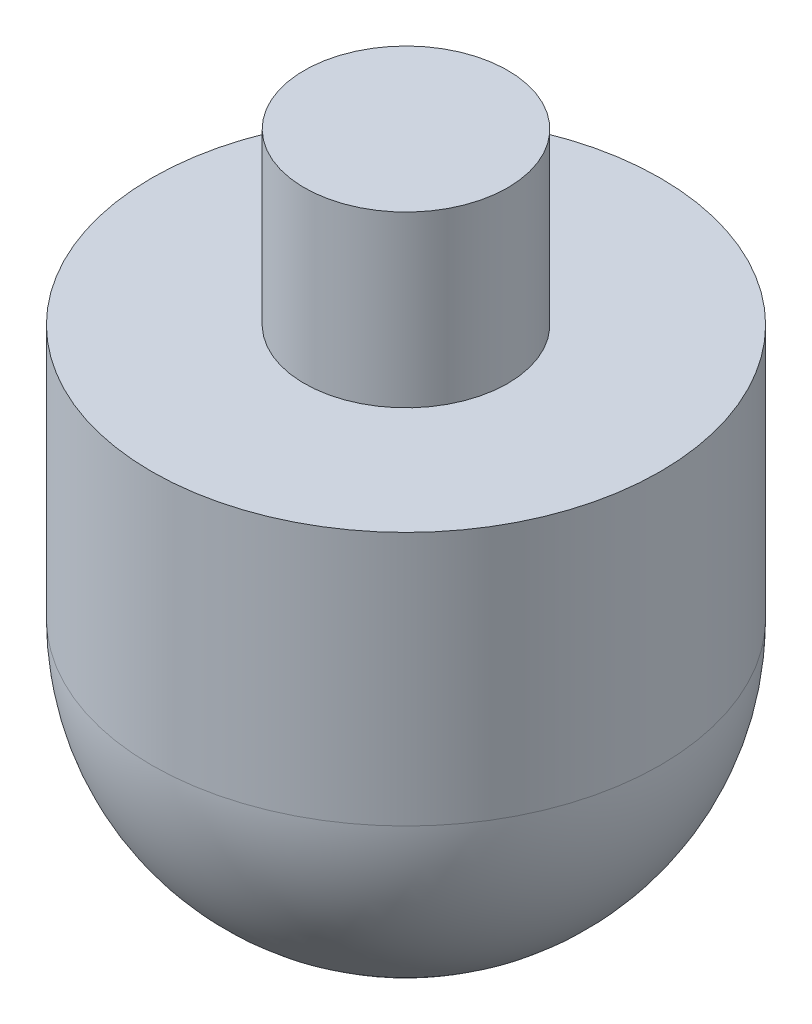
SolidWorks part; units mm, degrees
ref_plane "Front Plane" through (0, 0, 0) normal (0, 0, 1) x (1, 0, 0)
ref_plane "Top Plane" through (0, 0, 0) normal (0, 1, 0) x (1, 0, 0)
ref_plane "Right Plane" through (0, 0, 0) normal (1, 0, 0) x (0, 0, -1)
sketch "Sketch1" plane through (0, 0, 0) normal (0, 0, 1) x (1, 0, 0)
  line L0 (0, 25) -> (0, 41.3952) construction
  line L1 (0, 25) -> (0, -15)
  line L2 (15, 0) -> (15, 15)
  line L3 (15, 15) -> (6, 15)
  line L4 (6, 15) -> (6, 25)
  line L5 (6, 25) -> (0, 25)
  arc A0 (0, -15) -> (15, 0) centre (0, 0) ccw
  dimension "D3" = 10
  dimension "D1" = 25
  dimension "D2" = 12
  dimension "D4" = 30
revolve "Revolve2" add sketch "Sketch1" angle 360 about L0
